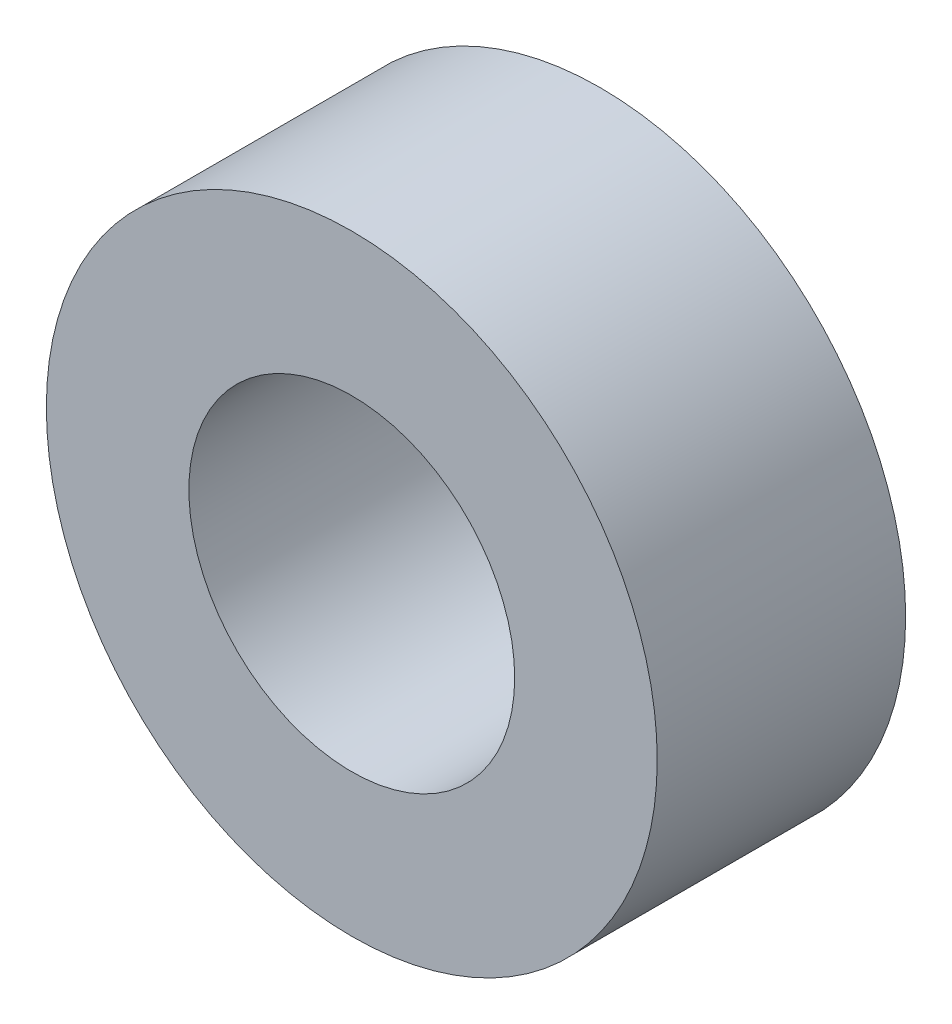
SolidWorks part; units mm, degrees
ref_plane "Alzado" through (0, 0, 0) normal (0, 0, 1) x (1, 0, 0)
ref_plane "Planta" through (0, 0, 0) normal (0, 1, 0) x (1, 0, 0)
ref_plane "Vista lateral" through (0, 0, 0) normal (1, 0, 0) x (0, 0, -1)
sketch "Croquis1" plane through (0, 0, 0) normal (0, 0, 1) x (1, 0, 0)
  circle A0 centre (0, 0) radius 4
  circle A1 centre (0, 0) radius 7.5
  dimension "D1" = 8
  dimension "D2" = 15
extrude "Saliente-Extruir1" add sketch "Croquis1" along normal blind 6.1
